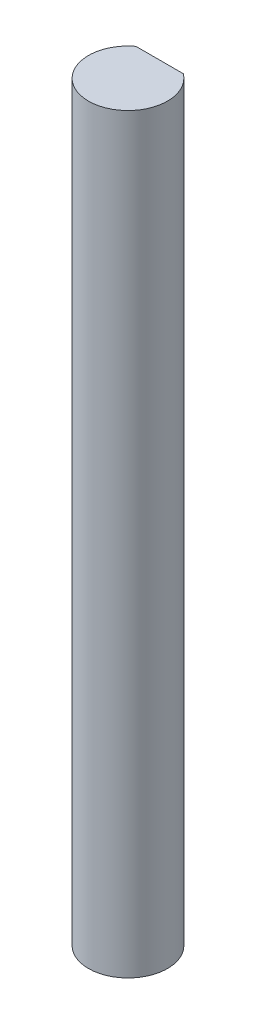
SolidWorks part; units mm, degrees
ref_plane "Front Plane" through (0, 0, 0) normal (0, 0, 1) x (1, 0, 0)
ref_plane "Top Plane" through (0, 0, 0) normal (0, 1, 0) x (1, 0, 0)
ref_plane "Right Plane" through (0, 0, 0) normal (1, 0, 0) x (0, 0, -1)
sketch "Sketch1" plane through (0, 0, 0) normal (0, 1, 0) x (1, 0, 0)
  line L0 (-1.905, 2.54) -> (1.905, 2.54)
  arc A0 (-1.905, 2.54) -> (1.905, 2.54) centre (0, 0) ccw
  dimension "D1" = 6.35
  dimension "D2" = 2.54
extrude "Boss-Extrude1" add sketch "Sketch1" along normal blind 60.325
